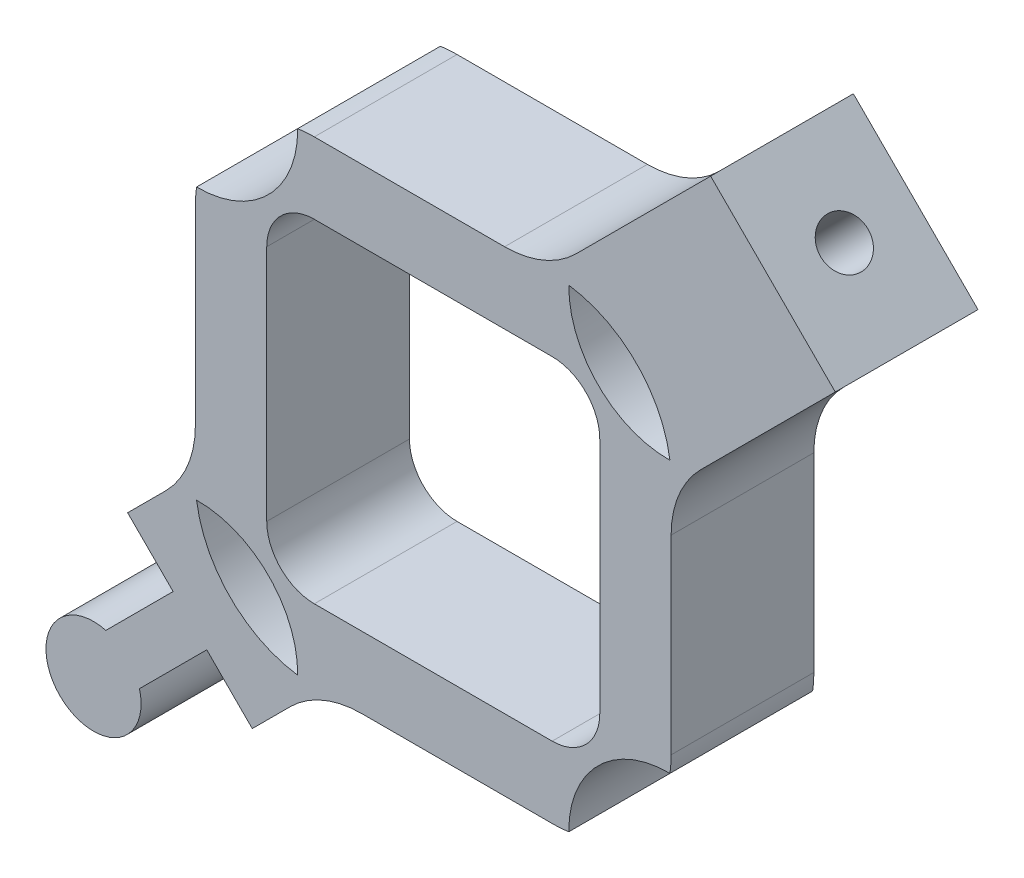
SolidWorks part; units mm, degrees
ref_plane "前视基准面" through (0, 0, 0) normal (0, 0, 1) x (1, 0, 0)
ref_plane "上视基准面" through (0, 0, 0) normal (0, 1, 0) x (1, 0, 0)
ref_plane "右视基准面" through (0, 0, 0) normal (1, 0, 0) x (0, 0, -1)
sketch "草图1" plane through (0, 0, 0) normal (0, 0, 1) x (1, 0, 0)
  line L0 (-5, 2.5) -> (-5, -2.5)
  line L1 (-2.5, 3.5) -> (2.5, 3.5)
  line L2 (-3.5, 2.5) -> (-3.5, -2.5)
  line L3 (-2.5, -3.5) -> (2.5, -3.5)
  line L4 (3.5, 2.5) -> (3.5, -2.5)
  line L5 (-3.5, 3.5) -> (3.5, -3.5) construction
  line L6 (-3.5, -3.5) -> (3.5, 3.5) construction
  line L7 (-2.5, -5) -> (2.5, -5)
  line L8 (5, 2.5) -> (5, -2.5)
  line L9 (-2.5, 5) -> (2.5, 5)
  line L10 (1.5, 5) -> (1.5, 7.9864) construction
  line L11 (1.5, 7.125) -> (3.0026, 5.6224) construction
  line L12 (3.0026, 5.6224) -> (5.831, 8.4508)
  line L13 (5.6224, 3.0026) -> (8.4508, 5.831)
  line L14 (5.831, 8.4508) -> (8.4508, 5.831)
  line L15 (-8.4508, -5.831) -> (-5.831, -8.4508)
  line L16 (-3.0026, -5.6224) -> (-5.831, -8.4508)
  line L17 (-5.6224, -3.0026) -> (-8.4508, -5.831)
  arc A0 (-3.5, -2.5) -> (-2.5, -3.5) centre (-2.5, -2.5) ccw
  arc A1 (2.5, -3.5) -> (3.5, -2.5) centre (2.5, -2.5) ccw
  arc A2 (3.5, 2.5) -> (2.5, 3.5) centre (2.5, 2.5) ccw
  arc A3 (-2.5, 3.5) -> (-3.5, 2.5) centre (-2.5, 2.5) ccw
  arc A4 (-5, -2.5) -> (-2.5, -5) centre (-2.5, -2.5) ccw
  arc A5 (2.5, -5) -> (2.8499, -4.9754) centre (2.5, -2.5) ccw
  arc A6 (5, 2.5) -> (2.5, 5) centre (2.5, 2.5) ccw
  arc A7 (-2.5, 5) -> (-2.8499, 4.9754) centre (-2.5, 2.5) ccw
  arc A8 (-4.9754, 2.8499) -> (-2.8499, 4.9754) centre (-4.9497, 4.9497) ccw
  arc A9 (-4.9754, 2.8499) -> (-5, 2.5) centre (-2.5, 2.5) ccw
  arc A10 (-2.5, 5) -> (-5, 2.5) centre (-2.5, 2.5) ccw construction
  arc A11 (4.9754, -2.8499) -> (2.8499, -4.9754) centre (4.9497, -4.9497) ccw
  arc A12 (4.9754, -2.8499) -> (5, -2.5) centre (2.5, -2.5) ccw
  arc A13 (2.5, -5) -> (5, -2.5) centre (2.5, -2.5) ccw construction
  arc A14 (2.8499, 4.9754) -> (4.9754, 2.8499) centre (4.9497, 4.9497) ccw
  arc A15 (-4.9754, -2.8499) -> (-2.8499, -4.9754) centre (-4.9497, -4.9497) cw
  arc A16 (1.5, 5) -> (3.0026, 5.6224) centre (1.5, 7.125) ccw
  arc A17 (5, 1.5) -> (5.6224, 3.0026) centre (7.125, 1.5) cw
  arc A18 (-1.5, -5) -> (-3.0026, -5.6224) centre (-1.5, -7.125) ccw
  arc A19 (-5, -1.5) -> (-5.6224, -3.0026) centre (-7.125, -1.5) cw
  point P0 (0, 0)
  dimension "D3" = 1
  dimension "D6" = 4.2
  dimension "D7" = 4.2
  dimension "D9" = 4.2
  dimension "D12" = 4.25
  dimension "D1" = 7
  dimension "D2" = 7
  dimension "D5" = 7
  dimension "D8" = 7
  dimension "D10" = 7
  dimension "D11" = 1
  dimension "D13" = 45
  dimension "D14" = 4
  dimension "D4" = 1.5
extrude "凸台-拉伸1" add sketch "草图1" along normal blind 3 contours A4 A15 L7 A5 A11 A12 L8 A6 A14 L9 A7 A8 A9 L0 A3 L1 A2 L4 A1 L3 A0 L2 | L0 A19 L17 L15 L16 A18 L7 A4 | L8 A17 L13 L14 L12 A16 L9 A6
sketch "草图4" plane through (-7.1409, -7.1409, 0) normal (-0.7071, -0.7071, 0) x (0, 0, 1)
  line L4 (0, 1.8525) -> (0, -1.8525)
  line L5 (0, -1.8525) -> (3, -1.8525)
  line L6 (3, -1.8525) -> (3, 1.8525)
  line L7 (3, 1.8525) -> (0, 1.8525)
  line L8 (0, 1.8525) -> (0, -1.8525)
  line L9 (0, -1.8525) -> (3, -1.8525)
  line L10 (3, -1.8525) -> (3, 1.8525)
  line L11 (3, 1.8525) -> (0, 1.8525)
  dimension "D1" = 0
extrude "凸台-拉伸3" add sketch "草图4" along normal blind 1
sketch "草图6" plane through (7.1409, 7.1409, 0) normal (0.7071, 0.7071, 0) x (0, 0, -1)
  line L0 (-3, 0) -> (0, 0) construction
  line L1 (-3, 1.8525) -> (-3, -1.8525) construction
  circle A0 centre (-1.5, 0) radius 0.5
  dimension "D1" = 1
extrude "切除-拉伸2" cut sketch "草图6" against normal up to next
sketch "草图5" plane through (0, 0, 3) normal (0, 0, 1) x (1, 0, 0)
  line L0 (-7.848, -7.848) -> (7.1409, 7.1409) construction
  line L1 (-6.5381, -9.1579) -> (-9.1579, -6.5381) construction
  line L2 (5.831, 8.4508) -> (8.4508, 5.831) construction
  line L3 (-4.7608, -5.4679) -> (-5.4679, -4.7608)
  line L4 (-5.4679, -4.7608) -> (-6.8821, -6.175)
  line L5 (-5.4679, -4.7608) -> (-6.4242, -3.8044)
  line L6 (-5.6224, -3.0026) -> (-9.1579, -6.5381) construction
  line L7 (-6.4242, -3.8044) -> (-9.1579, -6.5381)
  line L8 (-9.1579, -6.5381) -> (-6.5381, -9.1579)
  line L9 (-4.7608, -5.4679) -> (-6.175, -6.8821)
  line L10 (-4.7608, -5.4679) -> (-3.8044, -6.4242)
  line L11 (-3.8044, -6.4242) -> (-6.5381, -9.1579)
  circle A0 centre (-7.1409, -7.1409) radius 1
  point P17 (-5.1143, -5.1143)
  line M27 (-5.6224, -3.0026) -> (-9.1579, -6.5381)
  line M28 (-9.1579, -6.5381) -> (-6.5381, -9.1579)
  line M29 (-6.5381, -9.1579) -> (-3.0026, -5.6224)
  dimension "D1" = 2
  dimension "D2" = 0.5
  dimension "D3" = 2
extrude "切除-拉伸1" cut sketch "草图5" against normal blind 3 contours A0 L4 L5 M27 M28 | A0 L8 L10 L9 M29
